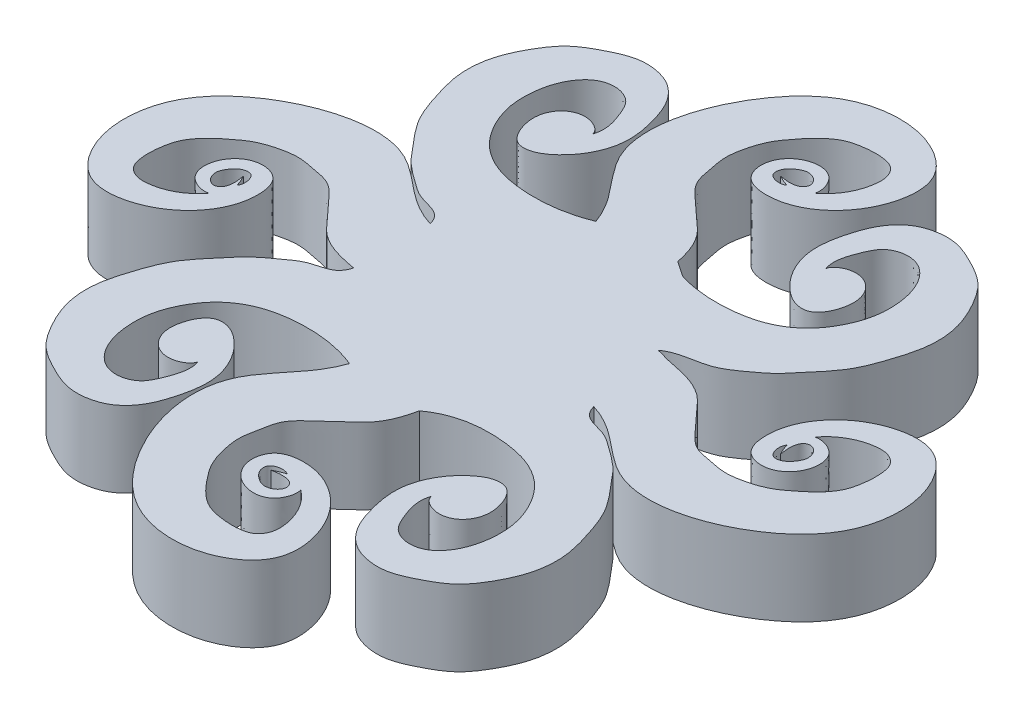
SolidWorks part; units mm, degrees
ref_plane "Front Plane" through (0, 0, 0) normal (0, 0, 1) x (1, 0, 0)
ref_plane "Top Plane" through (0, 0, 0) normal (0, 1, 0) x (1, 0, 0)
ref_plane "Right Plane" through (0, 0, 0) normal (1, 0, 0) x (0, 0, -1)
sketch "Sketch1" plane through (0, 0, 0) normal (0, 1, 0) x (1, 0, 0)
  line L0 (-137.5221, 312.9661) -> (42.0831, 492.5712) construction
  line L1 (0, 0) -> (100, 0)
  line L2 (0, 0) -> (0, 100)
  line L3 (0, 100) -> (100, 100)
  line L4 (100, 0) -> (100, 100)
  line L5 (0, 50) -> (100, 50) construction
  line L6 (50, 100) -> (50, 0) construction
  line L7 (0, 0) -> (100, 0)
  line L8 (0, 100) -> (100, 100)
  line L9 (0, 0) -> (100, 100)
  line L10 (0, 100) -> (100, 0)
  circle A0 centre (50, 50) radius 11
  spline S0 degree 3 poles (41.8661, 57.4054) (46.701, 61.1096) (45.1353, 68.2538) (35.8651, 77.0149) (39.534, 89.8969) (48.042, 98.1531) (57.0489, 98.3656) (63.2707, 93.2329) (62.2719, 86.5125) (58.4841, 81.8528) (53.9618, 80.0775) (49.6945, 80.8153) (48.8956, 84.5821) (51.2739, 87.369) (56.7979, 87.4647) (56.8692, 80.8999) (51.8214, 83.52) knots 0 0 0 0 0.130846 0.205908 0.373668 0.458524 0.563429 0.616002 0.684327 0.743989 0.794856 0.830051 0.857944 0.89521 0.928487 1 1 1 1
  spline S1 degree 3 poles (51.8214, 83.52) (52.472, 83.4079) (53.4015, 83.2628) (54.5829, 83.6983) (54.8837, 84.4198) (54.6621, 85.0586) (54.2169, 85.5067) (53.6439, 85.7228) (53.0512, 85.8036) (52.3837, 85.5614) (51.6885, 85.0892) (51.053, 84.3727) (50.8497, 82.6835) (52.804, 82.495) (53.2799, 82.9075) knots 0 0 0 0 0.166366 0.241726 0.299227 0.344909 0.407108 0.454045 0.499649 0.556761 0.630203 0.713357 0.798618 1 1 1 1
  spline S2 degree 3 poles (56.0389, 83.8395) (57.6208, 85.0131) (58.9873, 87.4073) (59.0345, 90.5343) (58.0896, 91.9736) (56.2517, 92.4492) (54.2472, 92.3528) (52.0283, 91.9307) (50.1178, 90.5672) (48.5985, 88.7801) (47.0469, 86.6832) (46.326, 84.3273) (45.9316, 81.9129) (46.4498, 79.6692) (46.8136, 77.1078) (48.8758, 75.2303) (50.9325, 73.3151) (53.6539, 71.081) (54.6991, 67.8956) (55.1151, 65.2419) (55.889, 63.2218) (55.1431, 59.3575) (58.2485, 58.4927) (59.1083, 56.1675) knots 0 0 0 0 0.103134 0.133672 0.160055 0.18614 0.228667 0.265873 0.302526 0.349029 0.389123 0.438157 0.476951 0.515573 0.558652 0.60831 0.655131 0.7086 0.789325 0.822647 0.849802 0.902946 1 1 1 1
  spline S3 degree 3 poles (56.0389, 16.1605) (57.6208, 14.9869) (58.9873, 12.5927) (59.0345, 9.4657) (58.0896, 8.0264) (56.2517, 7.5508) (54.2472, 7.6472) (52.0283, 8.0693) (50.1178, 9.4328) (48.5985, 11.2199) (47.0469, 13.3168) (46.326, 15.6727) (45.9316, 18.0871) (46.4498, 20.3308) (46.8136, 22.8922) (48.8758, 24.7697) (50.9325, 26.6849) (53.6539, 28.919) (54.6991, 32.1044) (55.1151, 34.7581) (55.889, 36.7782) (55.1431, 40.6425) (58.2485, 41.5073) (59.1083, 43.8325) knots 0 0 0 0 0.103134 0.133672 0.160055 0.18614 0.228667 0.265873 0.302526 0.349029 0.389123 0.438157 0.476951 0.515573 0.558652 0.60831 0.655131 0.7086 0.789325 0.822647 0.849802 0.902946 1 1 1 1
  spline S4 degree 3 poles (51.8214, 16.48) (52.472, 16.5921) (53.4015, 16.7372) (54.5829, 16.3017) (54.8837, 15.5802) (54.6621, 14.9414) (54.2169, 14.4933) (53.6439, 14.2772) (53.0512, 14.1964) (52.3837, 14.4386) (51.6885, 14.9108) (51.053, 15.6273) (50.8497, 17.3165) (52.804, 17.505) (53.2799, 17.0925) knots 0 0 0 0 0.166366 0.241726 0.299227 0.344909 0.407108 0.454045 0.499649 0.556761 0.630203 0.713357 0.798618 1 1 1 1
  spline S5 degree 3 poles (41.8661, 42.5946) (46.701, 38.8904) (45.1353, 31.7462) (35.8651, 22.9851) (39.534, 10.1031) (48.042, 1.8469) (57.0489, 1.6344) (63.2707, 6.7671) (62.2719, 13.4875) (58.4841, 18.1472) (53.9618, 19.9225) (49.6945, 19.1847) (48.8956, 15.4179) (51.2739, 12.631) (56.7979, 12.5353) (56.8692, 19.1001) (51.8214, 16.48) knots 0 0 0 0 0.130846 0.205908 0.373668 0.458524 0.563429 0.616002 0.684327 0.743989 0.794856 0.830051 0.857944 0.89521 0.928487 1 1 1 1
  spline S6 degree 3 poles (83.8395, 56.0389) (85.0131, 57.6208) (87.4073, 58.9873) (90.5343, 59.0345) (91.9736, 58.0896) (92.4492, 56.2517) (92.3528, 54.2472) (91.9307, 52.0283) (90.5672, 50.1178) (88.7801, 48.5985) (86.6832, 47.0469) (84.3273, 46.326) (81.9129, 45.9316) (79.6692, 46.4498) (77.1078, 46.8136) (75.2303, 48.8758) (73.3151, 50.9325) (71.081, 53.6539) (67.8956, 54.6991) (65.2419, 55.1151) (63.2218, 55.889) (59.3575, 55.1431) (58.4927, 58.2485) (56.1675, 59.1083) knots 0 0 0 0 0.103134 0.133672 0.160055 0.18614 0.228667 0.265873 0.302526 0.349029 0.389123 0.438157 0.476951 0.515573 0.558652 0.60831 0.655131 0.7086 0.789325 0.822647 0.849802 0.902946 1 1 1 1
  spline S7 degree 3 poles (83.52, 51.8214) (83.4079, 52.472) (83.2628, 53.4015) (83.6983, 54.5829) (84.4198, 54.8837) (85.0586, 54.6621) (85.5067, 54.2169) (85.7228, 53.6439) (85.8036, 53.0512) (85.5614, 52.3837) (85.0892, 51.6885) (84.3727, 51.053) (82.6835, 50.8497) (82.495, 52.804) (82.9075, 53.2799) knots 0 0 0 0 0.166366 0.241726 0.299227 0.344909 0.407108 0.454045 0.499649 0.556761 0.630203 0.713357 0.798618 1 1 1 1
  spline S8 degree 3 poles (57.4054, 41.8661) (61.1096, 46.701) (68.2538, 45.1353) (77.0149, 35.8651) (89.8969, 39.534) (98.1531, 48.042) (98.3656, 57.0489) (93.2329, 63.2707) (86.5125, 62.2719) (81.8528, 58.4841) (80.0775, 53.9618) (80.8153, 49.6945) (84.5821, 48.8956) (87.369, 51.2739) (87.4647, 56.7979) (80.8999, 56.8692) (83.52, 51.8214) knots 0 0 0 0 0.130846 0.205908 0.373668 0.458524 0.563429 0.616002 0.684327 0.743989 0.794856 0.830051 0.857944 0.89521 0.928487 1 1 1 1
  spline S9 degree 3 poles (16.1605, 43.9611) (14.9869, 42.3792) (12.5927, 41.0127) (9.4657, 40.9655) (8.0264, 41.9104) (7.5508, 43.7483) (7.6472, 45.7528) (8.0693, 47.9717) (9.4328, 49.8822) (11.2199, 51.4015) (13.3168, 52.9531) (15.6727, 53.674) (18.0871, 54.0684) (20.3308, 53.5502) (22.8922, 53.1864) (24.7697, 51.1242) (26.6849, 49.0675) (28.919, 46.3461) (32.1044, 45.3009) (34.7581, 44.8849) (36.7782, 44.111) (40.6425, 44.8569) (41.5073, 41.7515) (43.8325, 40.8917) knots 0 0 0 0 0.103134 0.133672 0.160055 0.18614 0.228667 0.265873 0.302526 0.349029 0.389123 0.438157 0.476951 0.515573 0.558652 0.60831 0.655131 0.7086 0.789325 0.822647 0.849802 0.902946 1 1 1 1
  spline S10 degree 3 poles (16.48, 48.1786) (16.5921, 47.528) (16.7372, 46.5985) (16.3017, 45.4171) (15.5802, 45.1163) (14.9414, 45.3379) (14.4933, 45.7831) (14.2772, 46.3561) (14.1964, 46.9488) (14.4386, 47.6163) (14.9108, 48.3115) (15.6273, 48.947) (17.3165, 49.1503) (17.505, 47.196) (17.0925, 46.7201) knots 0 0 0 0 0.166366 0.241726 0.299227 0.344909 0.407108 0.454045 0.499649 0.556761 0.630203 0.713357 0.798618 1 1 1 1
  spline S11 degree 3 poles (42.5946, 58.1339) (38.8904, 53.299) (31.7462, 54.8647) (22.9851, 64.1349) (10.1031, 60.466) (1.8469, 51.958) (1.6344, 42.9511) (6.7671, 36.7293) (13.4875, 37.7281) (18.1472, 41.5159) (19.9225, 46.0382) (19.1847, 50.3055) (15.4179, 51.1044) (12.631, 48.7261) (12.5353, 43.2021) (19.1001, 43.1308) (16.48, 48.1786) knots 0 0 0 0 0.130846 0.205908 0.373668 0.458524 0.563429 0.616002 0.684327 0.743989 0.794856 0.830051 0.857944 0.89521 0.928487 1 1 1 1
  spline S12 degree 3 poles (34.1884, 55.0434) (33.7016, 56.952) (30.9574, 56.8848) (28.119, 59.0296) (25.8782, 60.6685) (24.4047, 62.5739) (22.9411, 64.2057) (21.2354, 66.5202) (19.9851, 69.9916) (18.8891, 73.7521) (19.1559, 78.0048) (20.6589, 81.3054) (22.856, 84.5531) (25.899, 86.2636) (29.0199, 87.6795) (31.6929, 87.4706) (34.0752, 86.6383) (36.0255, 84.6259) (37.3044, 81.094) (38.2341, 76.3029) (36.0509, 72.3163) (33.8855, 70.5907) (32.6952, 69.8934) (30.9599, 69.6378) (29.7374, 70.891) (29.1677, 72.2055) (28.8482, 73.6602) (29.0518, 75.3626) (29.9773, 76.7405) (31.6842, 77.5967) (33.4225, 77.3986) (34.8521, 76.2044) (34.4451, 74.5803) (33.1722, 73.0823) (31.7022, 72.0226) (30.9569, 73.9879) knots 0 0 0 0 0.047267 0.084492 0.118113 0.141185 0.165634 0.192609 0.23794 0.28982 0.324183 0.379899 0.410854 0.455212 0.495953 0.524737 0.543497 0.580828 0.61431 0.670605 0.741153 0.752797 0.764261 0.788348 0.80436 0.819459 0.83697 0.854154 0.876413 0.889807 0.917327 0.931105 0.946423 0.966659 1 1 1 1
  spline S13 degree 3 poles (30.9569, 73.9879) (31.3845, 73.6785) (32.0299, 73.2113) (32.6853, 74.0624) (33.1102, 74.5719) (33.2738, 75.5172) (32.4237, 75.582) (31.7947, 75.4427) (31.327, 74.9826) (31.0485, 74.5027) (31.0389, 74.1446) (31.0336, 73.9436) knots 0 0 0 0 0.196597 0.29679 0.42697 0.538886 0.618953 0.750864 0.838714 0.909458 1 1 1 1
  spline S14 degree 3 poles (34.6468, 75.9336) (35.142, 77.3591) (34.4579, 79.442) (33.2298, 82.1516) (31.0419, 83.025) (28.7234, 82.5288) (26.7995, 80.4721) (25.7888, 77.1866) (25.8688, 73.6034) (27.1487, 70.3459) (29.1087, 67.5711) (32.2246, 65.6685) (37.6211, 64.5305) (41.9508, 65.0286) (44.8279, 66.2176) knots 0 0 0 0 0.099619 0.145832 0.199041 0.246529 0.301572 0.38394 0.478276 0.542636 0.623024 0.708169 0.787047 1 1 1 1
  spline S15 degree 3 poles (34.6468, 24.0664) (35.142, 22.6409) (34.4579, 20.558) (33.2298, 17.8484) (31.0419, 16.975) (28.7234, 17.4712) (26.7995, 19.5279) (25.7888, 22.8134) (25.8688, 26.3966) (27.1487, 29.6541) (29.1087, 32.4289) (32.2246, 34.3315) (37.6211, 35.4695) (41.9508, 34.9714) (44.8279, 33.7824) knots 0 0 0 0 0.099619 0.145832 0.199041 0.246529 0.301572 0.38394 0.478276 0.542636 0.623024 0.708169 0.787047 1 1 1 1
  spline S16 degree 3 poles (30.9569, 26.0121) (31.3845, 26.3215) (32.0299, 26.7887) (32.6853, 25.9376) (33.1102, 25.4281) (33.2738, 24.4828) (32.4237, 24.418) (31.7947, 24.5573) (31.327, 25.0174) (31.0485, 25.4973) (31.0389, 25.8554) (31.0336, 26.0564) knots 0 0 0 0 0.196597 0.29679 0.42697 0.538886 0.618953 0.750864 0.838714 0.909458 1 1 1 1
  spline S17 degree 3 poles (34.1884, 44.9566) (33.7016, 43.048) (30.9574, 43.1152) (28.119, 40.9704) (25.8782, 39.3315) (24.4047, 37.4261) (22.9411, 35.7943) (21.2354, 33.4798) (19.9851, 30.0084) (18.8891, 26.2479) (19.1559, 21.9952) (20.6589, 18.6946) (22.856, 15.4469) (25.899, 13.7364) (29.0199, 12.3205) (31.6929, 12.5294) (34.0752, 13.3617) (36.0255, 15.3741) (37.3044, 18.906) (38.2341, 23.6971) (36.0509, 27.6837) (33.8855, 29.4093) (32.6952, 30.1066) (30.9599, 30.3622) (29.7374, 29.109) (29.1677, 27.7945) (28.8482, 26.3398) (29.0518, 24.6374) (29.9773, 23.2595) (31.6842, 22.4033) (33.4225, 22.6014) (34.8521, 23.7956) (34.4451, 25.4197) (33.1722, 26.9177) (31.7022, 27.9774) (30.9569, 26.0121) knots 0 0 0 0 0.047267 0.084492 0.118113 0.141185 0.165634 0.192609 0.23794 0.28982 0.324183 0.379899 0.410854 0.455212 0.495953 0.524737 0.543497 0.580828 0.61431 0.670605 0.741153 0.752797 0.764261 0.788348 0.80436 0.819459 0.83697 0.854154 0.876413 0.889807 0.917327 0.931105 0.946423 0.966659 1 1 1 1
  spline S18 degree 3 poles (69.0431, 26.0121) (68.6155, 26.3215) (67.9701, 26.7887) (67.3147, 25.9376) (66.8898, 25.4281) (66.7262, 24.4828) (67.5763, 24.418) (68.2053, 24.5573) (68.673, 25.0174) (68.9515, 25.4973) (68.9611, 25.8554) (68.9664, 26.0564) knots 0 0 0 0 0.196597 0.29679 0.42697 0.538886 0.618953 0.750864 0.838714 0.909458 1 1 1 1
  spline S19 degree 3 poles (65.8116, 44.9566) (66.2984, 43.048) (69.0426, 43.1152) (71.881, 40.9704) (74.1218, 39.3315) (75.5953, 37.4261) (77.0589, 35.7943) (78.7646, 33.4798) (80.0149, 30.0084) (81.1109, 26.2479) (80.8441, 21.9952) (79.3411, 18.6946) (77.144, 15.4469) (74.101, 13.7364) (70.9801, 12.3205) (68.3071, 12.5294) (65.9248, 13.3617) (63.9745, 15.3741) (62.6956, 18.906) (61.7659, 23.6971) (63.9491, 27.6837) (66.1145, 29.4093) (67.3048, 30.1066) (69.0401, 30.3622) (70.2626, 29.109) (70.8323, 27.7945) (71.1518, 26.3398) (70.9482, 24.6374) (70.0227, 23.2595) (68.3158, 22.4033) (66.5775, 22.6014) (65.1479, 23.7956) (65.5549, 25.4197) (66.8278, 26.9177) (68.2978, 27.9774) (69.0431, 26.0121) knots 0 0 0 0 0.047267 0.084492 0.118113 0.141185 0.165634 0.192609 0.23794 0.28982 0.324183 0.379899 0.410854 0.455212 0.495953 0.524737 0.543497 0.580828 0.61431 0.670605 0.741153 0.752797 0.764261 0.788348 0.80436 0.819459 0.83697 0.854154 0.876413 0.889807 0.917327 0.931105 0.946423 0.966659 1 1 1 1
  spline S20 degree 3 poles (65.3532, 24.0664) (64.858, 22.6409) (65.5421, 20.558) (66.7702, 17.8484) (68.9581, 16.975) (71.2766, 17.4712) (73.2005, 19.5279) (74.2111, 22.8134) (74.1312, 26.3966) (72.8513, 29.6543) (70.8916, 32.428) (67.7742, 34.3349) (62.19, 35.4897) (57.5965, 35.0583) (54.8067, 32.9931) knots 0 0 0 0 0.098274 0.143863 0.196353 0.2432 0.297499 0.378754 0.471816 0.535307 0.614609 0.698604 0.776417 1 1 1 1
  spline S21 degree 1 poles (56.8387, 65.6495) (54.8067, 67.0069) knots 0 0 1 1
  spline S22 degree 1 poles (63.6193, 55.6152) (63.647, 55.6108) knots 0 0 1 1
  spline S24 degree 3 poles (69.0431, 73.9879) (68.6155, 73.6785) (67.9701, 73.2113) (67.3147, 74.0624) (66.8898, 74.5719) (66.7262, 75.5172) (67.5763, 75.582) (68.2053, 75.4427) (68.673, 74.9826) (68.9515, 74.5027) (68.9611, 74.1446) (68.9664, 73.9436) knots 0 0 0 0 0.196597 0.29679 0.42697 0.538886 0.618953 0.750864 0.838714 0.909458 1 1 1 1
  spline S25 degree 3 poles (65.3532, 75.9336) (64.858, 77.3591) (65.5421, 79.442) (66.7702, 82.1516) (68.9581, 83.025) (71.2766, 82.5288) (73.2005, 80.4721) (74.2112, 77.1866) (74.1312, 73.6034) (72.8513, 70.3459) (70.8913, 67.5712) (67.7753, 65.6682) (62.9562, 64.654) (59.2391, 64.9085) (56.8387, 65.6495) knots 0 0 0 0 0.103801 0.151955 0.207397 0.256879 0.314232 0.400058 0.498354 0.565416 0.649179 0.737898 0.820088 1 1 1 1
  spline S26 degree 3 poles (63.6193, 55.6152) (65.2177, 56.808) (68.5661, 56.6167) (71.8877, 59.0178) (74.1207, 60.6705) (75.5956, 62.5734) (77.0588, 64.2059) (78.7646, 66.5201) (80.0149, 69.9916) (81.1109, 73.7521) (80.8441, 78.0048) (79.3411, 81.3054) (77.144, 84.5531) (74.101, 86.2636) (70.9801, 87.6795) (68.3071, 87.4706) (65.9248, 86.6383) (63.9745, 84.6259) (62.6956, 81.094) (61.7659, 76.3029) (63.9491, 72.3163) (66.1145, 70.5907) (67.3048, 69.8934) (69.0401, 69.6378) (70.2626, 70.891) (70.8323, 72.2055) (71.1518, 73.6602) (70.9482, 75.3626) (70.0227, 76.7405) (68.3158, 77.5967) (66.5775, 77.3986) (65.1479, 76.2044) (65.5549, 74.5803) (66.8278, 73.0823) (68.2978, 72.0226) (69.0431, 73.9879) knots 0 0 0 0 0.06439 0.100946 0.133963 0.15662 0.18063 0.20712 0.251637 0.302584 0.336329 0.391044 0.421443 0.465004 0.505012 0.533278 0.551701 0.588362 0.621242 0.676525 0.745805 0.75724 0.768498 0.792152 0.807877 0.822703 0.8399 0.856775 0.878634 0.891787 0.918813 0.932343 0.947386 0.967258 1 1 1 1
  point P411 (34.1884, 44.9567)
  point P412 (65.8116, 44.9566)
  point P413 (54.8067, 32.9931)
  point P414 (63.6193, 55.6152)
  point P415 (0, 0)
  dimension "D3" = 22
  dimension "D1" = 100
  dimension "D2" = 100
extrude "Boss-Extrude2" add sketch "Sketch1" along normal blind 10
sketch "Sketch2" plane through (0, 0, 0) normal (0, 1, 0) x (1, 0, 0)
  line L6 (114.7807, 107.9462) -> (-12.1083, -9.8394) construction
  circle A0 centre (51.3362, 49.0534) radius 13.1665
  point P0 (51.3362, 49.0534)
extrude "Boss-Extrude4" add sketch "Sketch2" along normal blind 10
sketch "Sketch4" plane through (0, 10, 0) normal (0, 1, 0) x (1, 0, 0)
  circle A0 centre (50.657, 49.4232) radius 11
  dimension "D1" = 22
